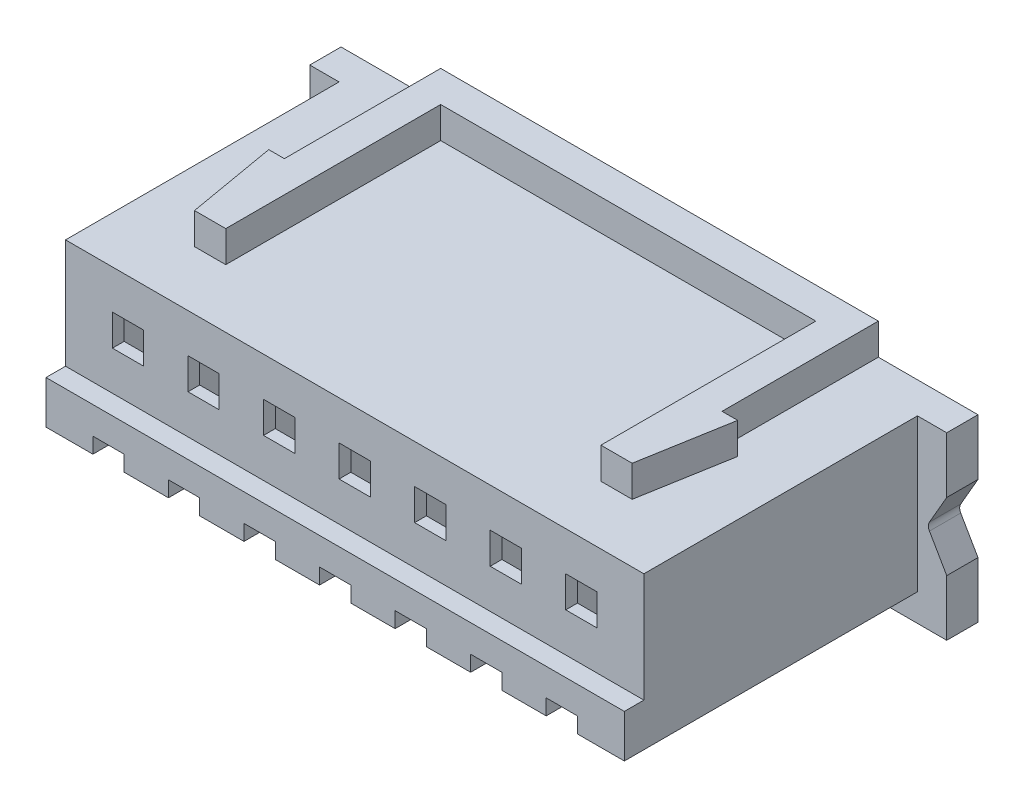
SolidWorks part; units mm, degrees
ref_plane "Front Plane" through (0, 0, 0) normal (0, 0, 1) x (1, 0, 0)
ref_plane "Top Plane" through (0, 0, 0) normal (0, 1, 0) x (1, 0, 0)
ref_plane "Right Plane" through (0, 0, 0) normal (1, 0, 0) x (0, 0, -1)
sketch "Sketch1" plane through (0, 0, 0) normal (0, 0, 1) x (1, 0, 0)
  line L1 (-7.4, -2.15) -> (7.4, -2.15)
  line L2 (-7.4, -2.15) -> (-7.4, 2.15)
  line L3 (-7.4, 2.15) -> (7.4, 2.15)
  line L4 (7.4, -2.15) -> (7.4, 2.15)
  line L5 (-7.4, -2.15) -> (7.4, 2.15) construction
  line L6 (-7.4, 2.15) -> (7.4, -2.15) construction
  point P0 (0, 0)
  dimension "D1" = 4.3
  dimension "D2" = 14.8
extrude "Boss-Extrude1" add sketch "Sketch1" along normal blind 7
sketch "Sketch2" plane through (0, 0, 0) normal (0, 0, -1) x (-1, 0, 0)
  line L0 (0, 0) -> (0, 2.15) construction
  line L1 (-8.15, 2.15) -> (8.15, 2.15)
  line L2 (-8.15, 2.15) -> (-8.15, -2.45)
  line L3 (-8.15, -2.45) -> (8.15, -2.45)
  line L4 (8.15, 2.15) -> (8.15, -2.45)
  dimension "D1" = 16.3
  dimension "D2" = 4.6
extrude "Boss-Extrude2" add sketch "Sketch2" along normal blind 0.8
sketch "Sketch3" plane through (0, 0, 0) normal (0, 0, 1) x (1, 0, 0)
  line L1 (8.15, 2.15) -> (8.15, -2.45) construction
  line L2 (7.65, -0.15) -> (8.15, -1.016)
  line L3 (7.65, -0.15) -> (8.15, 0.716)
  line L4 (8.15, -0.15) -> (7.65, -0.15) construction
  line L5 (8.15, 0.716) -> (8.15, -1.016)
  dimension "D1" = 60
  dimension "D2" = 0.5
  dimension "D3" = 60
extrude "Cut-Extrude1" cut sketch "Sketch3" against normal blind 1
fillet "Fillet1" radius 0.2 1 edges at (7.65, -0.15, -0.4)
sketch "Sketch4" plane through (0, 0, 7) normal (0, 0, 1) x (1, 0, 0)
  line L0 (-7.4, 2.15) -> (-7.4, -2.15) construction
  line L1 (-7.4, -0.65) -> (7.4, -0.65)
  line L2 (-7.4, -0.65) -> (-7.4, -2.15)
  line L3 (-7.4, -2.15) -> (7.4, -2.15)
  line L4 (7.4, -0.65) -> (7.4, -2.15)
  dimension "D1" = 1.5
extrude "Boss-Extrude3" add sketch "Sketch4" along normal blind 0.5
sketch "Sketch5" plane through (0, 0, 7.5) normal (0, 0, 1) x (1, 0, 0)
  line L0 (4.2667, -1.35) -> (4.2667, -2.15)
  line L1 (3.4667, -1.35) -> (4.2667, -1.35)
  line L2 (3.4667, -1.35) -> (3.4667, -2.15)
  line L3 (3.4667, -2.15) -> (4.2667, -2.15)
  line L4 (2.3333, -1.35) -> (2.3333, -2.15)
  line L5 (1.5333, -1.35) -> (2.3333, -1.35)
  line L6 (1.5333, -1.35) -> (1.5333, -2.15)
  line L7 (1.5333, -2.15) -> (2.3333, -2.15)
  line L8 (0.4, -1.35) -> (0.4, -2.15)
  line L9 (-0.4, -1.35) -> (0.4, -1.35)
  line L10 (-0.4, -1.35) -> (-0.4, -2.15)
  line L11 (-0.4, -2.15) -> (0.4, -2.15)
  line L12 (-1.5333, -1.35) -> (-1.5333, -2.15)
  line L13 (-2.3333, -1.35) -> (-1.5333, -1.35)
  line L14 (5.4, -1.35) -> (6.2, -1.35)
  line L15 (6.2, -1.35) -> (6.2, -2.15)
  line L16 (5.4, -1.35) -> (5.4, -2.15)
  line L17 (5.4, -2.15) -> (6.2, -2.15)
  line L18 (7.4, -2.15) -> (7.4, -0.65) construction
  line L19 (-2.3333, -1.35) -> (-2.3333, -2.15)
  line L20 (-2.3333, -2.15) -> (-1.5333, -2.15)
  line L21 (-3.4667, -1.35) -> (-3.4667, -2.15)
  line L22 (-4.2667, -1.35) -> (-3.4667, -1.35)
  line L23 (-4.2667, -1.35) -> (-4.2667, -2.15)
  line L24 (-4.2667, -2.15) -> (-3.4667, -2.15)
  line L25 (-5.4, -1.35) -> (-5.4, -2.15)
  line L26 (-6.2, -1.35) -> (-5.4, -1.35)
  line L27 (-6.2, -1.35) -> (-6.2, -2.15)
  line L28 (-6.2, -2.15) -> (-5.4, -2.15)
  line L30 (-7.4, -0.65) -> (-7.4, -2.15) construction
  dimension "D1" = 0.8
  dimension "D2" = 0.8
  dimension "D3" = 7
  dimension "D5" = 1.2
  dimension "D4" = 1.2
extrude "Cut-Extrude2" cut sketch "Sketch5" against normal blind 3.2
sketch "Sketch6" plane through (0, 0, 7) normal (0, 0, 1) x (1, 0, 0)
  line L0 (-7.4, 2.15) -> (-7.4, -0.65) construction
  line L1 (-6.2, 1.15) -> (-5.4, 1.15)
  line L2 (-6.2, 1.15) -> (-6.2, 0.35)
  line L3 (-6.2, 0.35) -> (-5.4, 0.35)
  line L4 (-5.4, 1.15) -> (-5.4, 0.35)
  line L5 (-4.2667, 1.15) -> (-3.4667, 1.15)
  line L6 (-3.4667, 1.15) -> (-3.4667, 0.35)
  line L7 (-4.2667, 0.35) -> (-3.4667, 0.35)
  line L8 (-4.2667, 1.15) -> (-4.2667, 0.35)
  line L9 (-2.3333, 1.15) -> (-1.5333, 1.15)
  line L10 (-1.5333, 1.15) -> (-1.5333, 0.35)
  line L11 (-2.3333, 0.35) -> (-1.5333, 0.35)
  line L12 (-2.3333, 1.15) -> (-2.3333, 0.35)
  line L13 (-0.4, 1.15) -> (0.4, 1.15)
  line L14 (0.4, 1.15) -> (0.4, 0.35)
  line L15 (-0.4, 0.35) -> (0.4, 0.35)
  line L16 (-0.4, 1.15) -> (-0.4, 0.35)
  line L17 (1.5333, 1.15) -> (2.3333, 1.15)
  line L18 (7.4, 2.15) -> (-7.4, 2.15) construction
  line L19 (2.3333, 1.15) -> (2.3333, 0.35)
  line L20 (1.5333, 0.35) -> (2.3333, 0.35)
  line L21 (1.5333, 1.15) -> (1.5333, 0.35)
  line L22 (3.4667, 1.15) -> (4.2667, 1.15)
  line L23 (4.2667, 1.15) -> (4.2667, 0.35)
  line L24 (3.4667, 0.35) -> (4.2667, 0.35)
  line L25 (3.4667, 1.15) -> (3.4667, 0.35)
  line L26 (5.4, 1.15) -> (6.2, 1.15)
  line L28 (6.2, 1.15) -> (6.2, 0.35)
  line L29 (5.4, 0.35) -> (6.2, 0.35)
  line L30 (5.4, 1.15) -> (5.4, 0.35)
  line L31 (7.4, -0.65) -> (7.4, 2.15) construction
  dimension "D1" = 0.8
  dimension "D2" = 0.8
  dimension "D3" = 1.2
  dimension "D5" = 1.2
  dimension "D6" = 1
  dimension "D4" = 7
extrude "Cut-Extrude3" cut sketch "Sketch6" against normal blind 10
sketch "Sketch7" plane through (0, 2.15, 0) normal (0, 1, 0) x (1, 0, 0)
  line L0 (-5.6, -5.5) -> (-6, -3.2)
  line L1 (-6, -3.2) -> (-5.6, -3.2)
  line L2 (-5.6, -3.2) -> (-5.6, 0.8)
  line L3 (-8.15, 0.8) -> (8.15, 0.8) construction
  line L4 (-5.6, 0.8) -> (5.6, 0.8)
  line L5 (5.6, 0.8) -> (5.6, -3.2)
  line L6 (5.6, -3.2) -> (6, -3.2)
  line L7 (6, -3.2) -> (5.6, -5.5)
  line L8 (5.6, -5.5) -> (4.8, -5.5)
  line L9 (4.8, -5.5) -> (4.8, 0)
  line L10 (4.8, 0) -> (-4.8, 0)
  line L11 (-4.8, 0) -> (-4.8, -5.5)
  line L12 (-4.8, -5.5) -> (-5.6, -5.5)
  line L13 (0, 0) -> (0, 0.8) construction
  dimension "D1" = 0.8
  dimension "D2" = 0.8
  dimension "D3" = 0.8
  dimension "D4" = 0.8
  dimension "D5" = 1.2
  dimension "D6" = 4
  dimension "D7" = 2.3
  dimension "D8" = 4
  dimension "D9" = 1.2
  dimension "D10" = 0.8
  dimension "D11" = 11.2
extrude "Boss-Extrude4" add sketch "Sketch7" along normal blind 0.8
sketch "Sketch8" plane through (0, 0, -0.8) normal (0, 0, -1) x (-1, 0, 0)
  line L0 (4.8, 1.85) -> (2.9333, 1.85)
  line L1 (6.8, 1.85) -> (4.8667, 1.85)
  line L2 (6.8, 1.85) -> (6.8, -0.95)
  line L3 (6.2, -0.95) -> (6.2, -1.35)
  line L4 (4.8667, 1.85) -> (4.8667, -0.95)
  line L5 (6.8, -0.95) -> (6.2, -0.95)
  line L6 (6.2, -1.35) -> (5.4, -1.35)
  line L7 (5.4, -1.35) -> (5.4, -0.95)
  line L8 (5.4, -0.95) -> (4.8667, -0.95)
  line L9 (4.2667, -0.95) -> (4.2667, -1.35)
  line L10 (4.8, -0.95) -> (4.2667, -0.95)
  line L11 (4.2667, -1.35) -> (3.4667, -1.35)
  line L12 (4.8, 1.85) -> (4.8, -0.95)
  line L13 (3.4667, -1.35) -> (3.4667, -0.95)
  line L14 (3.4667, -0.95) -> (2.9333, -0.95)
  line L15 (2.8667, 1.85) -> (2.8667, -0.95)
  line L16 (2.8667, 1.85) -> (1, 1.85)
  line L17 (2.9333, 1.85) -> (2.9333, -0.95)
  line L18 (2.3333, -0.95) -> (2.3333, -1.35)
  line L19 (2.8667, -0.95) -> (2.3333, -0.95)
  line L20 (2.3333, -1.35) -> (1.5333, -1.35)
  line L21 (1.5333, -1.35) -> (1.5333, -0.95)
  line L22 (1.5333, -0.95) -> (1, -0.95)
  line L23 (0.9333, 1.85) -> (0.9333, -0.95)
  line L24 (0.9333, 1.85) -> (-0.9333, 1.85)
  line L25 (1, 1.85) -> (1, -0.95)
  line L26 (0.4, -0.95) -> (0.4, -1.35)
  line L27 (0.9333, -0.95) -> (0.4, -0.95)
  line L28 (0.4, -1.35) -> (-0.4, -1.35)
  line L29 (-0.4, -1.35) -> (-0.4, -0.95)
  line L30 (-0.4, -0.95) -> (-0.9333, -0.95)
  line L31 (-1, 1.85) -> (-1, -0.95)
  line L32 (-1, 1.85) -> (-2.8667, 1.85)
  line L33 (-0.9333, 1.85) -> (-0.9333, -0.95)
  line L34 (-1.5333, -0.95) -> (-1.5333, -1.35)
  line L35 (-1, -0.95) -> (-1.5333, -0.95)
  line L36 (-1.5333, -1.35) -> (-2.3333, -1.35)
  line L37 (-2.3333, -1.35) -> (-2.3333, -0.95)
  line L38 (-2.3333, -0.95) -> (-2.8667, -0.95)
  line L39 (-2.9333, 1.85) -> (-2.9333, -0.95)
  line L40 (-2.9333, 1.85) -> (-4.8, 1.85)
  line L41 (-2.8667, 1.85) -> (-2.8667, -0.95)
  line L42 (-3.4667, -0.95) -> (-3.4667, -1.35)
  line L43 (-2.9333, -0.95) -> (-3.4667, -0.95)
  line L44 (-3.4667, -1.35) -> (-4.2667, -1.35)
  line L45 (-4.2667, -1.35) -> (-4.2667, -0.95)
  line L46 (-4.2667, -0.95) -> (-4.8, -0.95)
  line L47 (-4.8667, 1.85) -> (-4.8667, -0.95)
  line L48 (-4.8667, 1.85) -> (-6.8, 1.85)
  line L49 (-4.8, 1.85) -> (-4.8, -0.95)
  line L50 (-5.4, -0.95) -> (-5.4, -1.35)
  line L51 (-4.8667, -0.95) -> (-5.4, -0.95)
  line L53 (4.2, -0.95) -> (4.2, -1.35) [skipped]
  line L55 (3.08, -0.95) -> (2.16, -0.95) [skipped]
  line L56 (3.4, -1.35) -> (3.4, -0.95) [skipped]
  line L57 (4.2, -1.35) -> (3.4, -1.35) [skipped]
  line L58 (2.2, -0.95) -> (2.2, -1.35) [skipped]
  line L59 (2.48, -0.95) -> (1.56, -0.95) [skipped]
  line L60 (2.8, 1.85) -> (2.8, -0.95) [skipped]
  line L61 (2.48, 1.85) -> (-0.16, 1.85) [skipped]
  line L63 (0.76, -0.95) -> (-0.16, -0.95) [skipped]
  line L64 (1.4, -1.35) -> (1.4, -0.95) [skipped]
  line L65 (2.2, -1.35) -> (1.4, -1.35) [skipped]
  line L66 (0.2, -0.95) -> (0.2, -1.35) [skipped]
  line L67 (0.16, -0.95) -> (-0.76, -0.95) [skipped]
  line L68 (0.8, 1.85) -> (0.8, -0.95) [skipped]
  line L69 (0.16, 1.85) -> (-2.48, 1.85) [skipped]
  line L71 (-1.56, -0.95) -> (-2.48, -0.95) [skipped]
  line L72 (-0.6, -1.35) -> (-0.6, -0.95) [skipped]
  line L73 (0.2, -1.35) -> (-0.6, -1.35) [skipped]
  line L74 (-1.8, -0.95) -> (-1.8, -1.35) [skipped]
  line L75 (-2.16, -0.95) -> (-3.08, -0.95) [skipped]
  line L76 (-1.2, 1.85) -> (-1.2, -0.95) [skipped]
  line L77 (-2.16, 1.85) -> (-4.8, 1.85) [skipped]
  line L79 (-3.88, -0.95) -> (-4.8, -0.95) [skipped]
  line L80 (-2.6, -1.35) -> (-2.6, -0.95) [skipped]
  line L81 (-1.8, -1.35) -> (-2.6, -1.35) [skipped]
  line L82 (-3.8, -0.95) -> (-3.8, -1.35) [skipped]
  line L83 (-4.48, -0.95) -> (-5.4, -0.95) [skipped]
  line L84 (-3.2, 1.85) -> (-3.2, -0.95) [skipped]
  line L85 (-4.48, 1.85) -> (-6.8, 1.85) [skipped]
  line L86 (-6.2, -0.95) -> (-6.8, -0.95) [skipped]
  line L87 (-4.6, -1.35) -> (-4.6, -0.95) [skipped]
  line L88 (-3.8, -1.35) -> (-4.6, -1.35) [skipped]
  line L90 (4.8, 1.85) -> (2.16, 1.85) [skipped]
  line L91 (4.8, -0.95) -> (3.88, -0.95) [skipped]
  line L92 (-5.4, -1.35) -> (-6.2, -1.35)
  line L93 (-6.2, -1.35) -> (-6.2, -0.95)
  line L94 (-6.2, -0.95) -> (-6.8, -0.95)
  line L95 (-6.8, 1.85) -> (-6.8, -0.95)
  line L97 (-8.15, 2.15) -> (-8.15, 0.716) construction
  dimension "D1" = 2.8
  dimension "D2" = 0.6
  dimension "D3" = 0.4
  dimension "D4" = 6
  dimension "D5" = 0.6
  dimension "D6" = 7
  dimension "D7" = 1.35
extrude "Cut-Extrude4" cut sketch "Sketch8" against normal blind 7.5
sketch "Sketch9" plane through (0, -2.15, 0) normal (0, -1, 0) x (1, 0, 0)
  line L20 (6.2, 4.3) -> (5.4, 4.3)
  line L21 (5.4, 4.3) -> (5.4, 7.5)
  line L22 (5.4, 7.5) -> (4.2667, 7.5)
  line L31 (-6.2, 7.5) -> (-7.4, 7.5)
  line L32 (-6.2, 7.5) -> (-7.4, 7.5)
  line L33 (-5.4, 4.3) -> (-6.2, 4.3)
  line L34 (-5.4, 4.3) -> (-6.2, 4.3)
  line L35 (-7.4, 7.5) -> (-7.4, 0)
  line L36 (-7.4, 0) -> (7.4, 0)
  line L37 (7.4, 0) -> (7.4, 7.5)
  line L38 (7.4, 7.5) -> (6.2, 7.5)
  line L39 (6.2, 7.5) -> (6.2, 4.3)
  line L40 (6.2, 4.3) -> (5.4, 4.3)
  line L41 (5.4, 4.3) -> (5.4, 7.5)
  line L42 (5.4, 7.5) -> (4.2667, 7.5)
  line L43 (-6.2, 4.3) -> (-6.2, 7.5)
  line L44 (-6.2, 4.3) -> (-6.2, 7.5)
  line L45 (4.2667, 7.5) -> (4.2667, 4.3)
  line L46 (4.2667, 7.5) -> (4.2667, 4.3)
  line L47 (4.2667, 4.3) -> (3.4667, 4.3)
  line L48 (4.2667, 4.3) -> (3.4667, 4.3)
  line L49 (3.4667, 4.3) -> (3.4667, 7.5)
  line L50 (3.4667, 4.3) -> (3.4667, 7.5)
  line L51 (3.4667, 7.5) -> (2.3333, 7.5)
  line L52 (3.4667, 7.5) -> (2.3333, 7.5)
  line L53 (2.3333, 7.5) -> (2.3333, 4.3)
  line L54 (2.3333, 7.5) -> (2.3333, 4.3)
  line L55 (-7.4, 7.5) -> (-7.4, 0)
  line L56 (-7.4, 0) -> (7.4, 0)
  line L57 (7.4, 0) -> (7.4, 7.5)
  line L58 (7.4, 7.5) -> (6.2, 7.5)
  line L59 (6.2, 7.5) -> (6.2, 4.3)
  line L60 (2.3333, 4.3) -> (1.5333, 4.3)
  line L61 (2.3333, 4.3) -> (1.5333, 4.3)
  line L62 (1.5333, 4.3) -> (1.5333, 7.5)
  line L63 (1.5333, 4.3) -> (1.5333, 7.5)
  line L64 (1.5333, 7.5) -> (0.4, 7.5)
  line L65 (1.5333, 7.5) -> (0.4, 7.5)
  line L66 (0.4, 7.5) -> (0.4, 4.3)
  line L67 (0.4, 7.5) -> (0.4, 4.3)
  line L68 (0.4, 4.3) -> (-0.4, 4.3)
  line L69 (0.4, 4.3) -> (-0.4, 4.3)
  line L70 (-0.4, 4.3) -> (-0.4, 7.5)
  line L71 (-0.4, 4.3) -> (-0.4, 7.5)
  line L72 (-0.4, 7.5) -> (-1.5333, 7.5)
  line L73 (-0.4, 7.5) -> (-1.5333, 7.5)
  line L74 (-1.5333, 7.5) -> (-1.5333, 4.3)
  line L75 (-1.5333, 7.5) -> (-1.5333, 4.3)
  line L76 (-1.5333, 4.3) -> (-2.3333, 4.3)
  line L77 (-1.5333, 4.3) -> (-2.3333, 4.3)
  line L78 (-2.3333, 4.3) -> (-2.3333, 7.5)
  line L79 (-2.3333, 4.3) -> (-2.3333, 7.5)
  line L80 (-2.3333, 7.5) -> (-3.4667, 7.5)
  line L81 (-2.3333, 7.5) -> (-3.4667, 7.5)
  line L82 (-3.4667, 7.5) -> (-3.4667, 4.3)
  line L83 (-3.4667, 7.5) -> (-3.4667, 4.3)
  line L88 (-3.4667, 4.3) -> (-4.2667, 4.3)
  line L89 (-3.4667, 4.3) -> (-4.2667, 4.3)
  line L90 (-4.2667, 4.3) -> (-4.2667, 7.5)
  line L91 (-4.2667, 4.3) -> (-4.2667, 7.5)
  line L92 (-4.2667, 7.5) -> (-5.4, 7.5)
  line L93 (-4.2667, 7.5) -> (-5.4, 7.5)
  line L94 (-5.4, 7.5) -> (-5.4, 4.3)
  line L95 (-5.4, 7.5) -> (-5.4, 4.3)
  dimension "D1" = 0
extrude "Cut-Extrude5" cut sketch "Sketch9" against normal blind 0.4
sketch "Sketch10" plane through (0, 0, -0.8) normal (0, 0, -1) x (-1, 0, 0)
  line L0 (-7.8546, -2.0157) -> (7.8538, -2.0157) construction
  text T0 "          1        2        3        4        5        6        7" font "Century Gothic" height 0.5
extrude "Boss-Extrude5" add sketch "Sketch10" along normal blind 0.1
